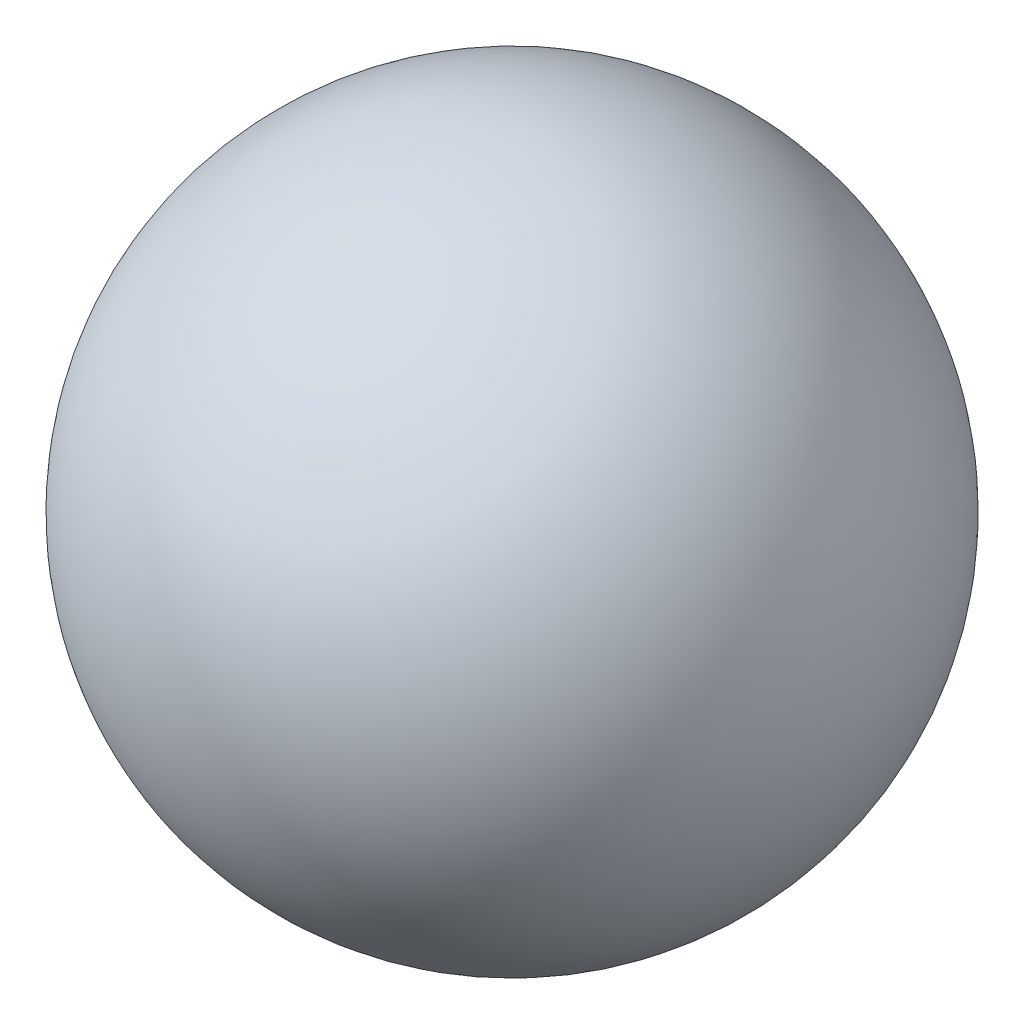
SolidWorks part; units mm, degrees
ref_plane "Front Plane" through (0, 0, 0) normal (0, 0, 1) x (1, 0, 0)
ref_plane "Horizon" through (0, 0, 0) normal (0, 1, 0) x (1, 0, 0)
ref_plane "0deg" through (0, 0, 0) normal (1, 0, 0) x (0, 0, -1)
sketch "Sketch1" plane through (0, 0, 0) normal (0, 1, 0) x (1, 0, 0)
  line L0 (0, -44.45) -> (0, 44.45)
  arc A0 (0, 42.45) -> (0, -42.45) centre (0, 0) ccw
  arc A1 (0, 44.45) -> (0, -44.45) centre (0, 0) ccw
  point P7 (0, 0)
  dimension "D1" = 88.9
  dimension "D2" = 2
revolve "Revolve1" add sketch "Sketch1" angle 360 about L0
sketch "Heading" plane through (0, 0, 0) normal (0, 1, 0) x (1, 0, 0)
  line L0 (0, 0) -> (0, -44.45)
  line L1 (0, 0) -> (-22.225, -38.4948) construction
  line L2 (0, 0) -> (-38.4948, -22.225) construction
  line L3 (0, 0) -> (-44.45, 0) construction
  line L4 (0, 0) -> (-38.4948, 22.225) construction
  line L5 (0, 0) -> (-22.225, 38.4948) construction
  line L6 (0, 0) -> (0, 44.45) construction
  line L7 (0, 0) -> (22.225, 38.4948) construction
  line L8 (0, 0) -> (38.4948, 22.225) construction
  line L9 (0, 0) -> (44.45, 0) construction
  line L10 (0, 0) -> (38.4948, -22.225) construction
  line L11 (0, 0) -> (22.225, -38.4948) construction
  line L12 (0, 0) -> (0, -44.45) construction
  line L13 (0, 0) -> (-22.225, -38.4948) construction
  circle A0 centre (0, 0) radius 44.45 construction
  dimension "D1" = 88.9
  dimension "D3" = 30
  dimension "D2" = 12
sketch "Pitch" plane through (0, 0, 0) normal (1, 0, 0) x (0, 0, -1)
  line L0 (0, 0) -> (38.4948, 22.225) construction
  line L1 (0, 0) -> (22.225, 38.4948) construction
  line L2 (0, 0) -> (0, 44.45) construction
  line L3 (0, 0) -> (-22.225, 38.4948) construction
  line L4 (0, 0) -> (-38.4948, 22.225) construction
  line L5 (0, 0) -> (-44.45, 0) construction
  line L6 (0, 0) -> (-38.4948, -22.225) construction
  line L7 (0, 0) -> (-22.225, -38.4948) construction
  line L8 (0, 0) -> (0, -44.45) construction
  line L9 (0, 0) -> (22.225, -38.4948) construction
  line L10 (0, 0) -> (38.4948, -22.225) construction
  line L11 (0, 0) -> (38.4948, 22.225) construction
  line L12 (0, 0) -> (22.225, 38.4948) construction
  circle A0 centre (0, 0) radius 44.45 construction
  dimension "D1" = 88.9
  dimension "D3" = 30
  dimension "D2" = 11
ref_plane "Hdg3" through (0, 0, 0) normal (-0.866, 0, 0.5) x (0.5, 0, 0.866)
ref_plane "Hdg6" through (0, 0, 0) normal (-0.5, 0, 0.866) x (0.866, 0, 0.5)
ref_plane "Hdg9" through (0, 0, 0) normal (0, 0, 1) x (1, 0, 0)
ref_plane "Hdg12" through (0, 0, 0) normal (0.5, 0, 0.866) x (0.866, 0, -0.5)
ref_plane "Hdg15" through (0, 0, 0) normal (0.866, 0, 0.5) x (0.5, 0, -0.866)
ref_plane "Hdg18" through (0, 0, 0) normal (1, 0, 0) x (0, 0, -1)
ref_plane "Hdg21" through (0, 0, 0) normal (0.866, 0, -0.5) x (-0.5, 0, -0.866)
ref_plane "Hdg24" through (0, 0, 0) normal (0.5, 0, -0.866) x (-0.866, 0, -0.5)
ref_plane "Hdg27" through (0, 0, 0) normal (0, 0, -1) x (-1, 0, 0)
ref_plane "Hdg30" through (0, 0, 0) normal (-0.5, 0, -0.866) x (-0.866, 0, 0.5)
ref_plane "Hdg33" through (0, 0, 0) normal (-0.866, 0, -0.5) x (-0.5, 0, 0.866)
ref_plane "Hdg0" through (0, 0, 0) normal (-1, 0, 0) x (0, 0, 1)
